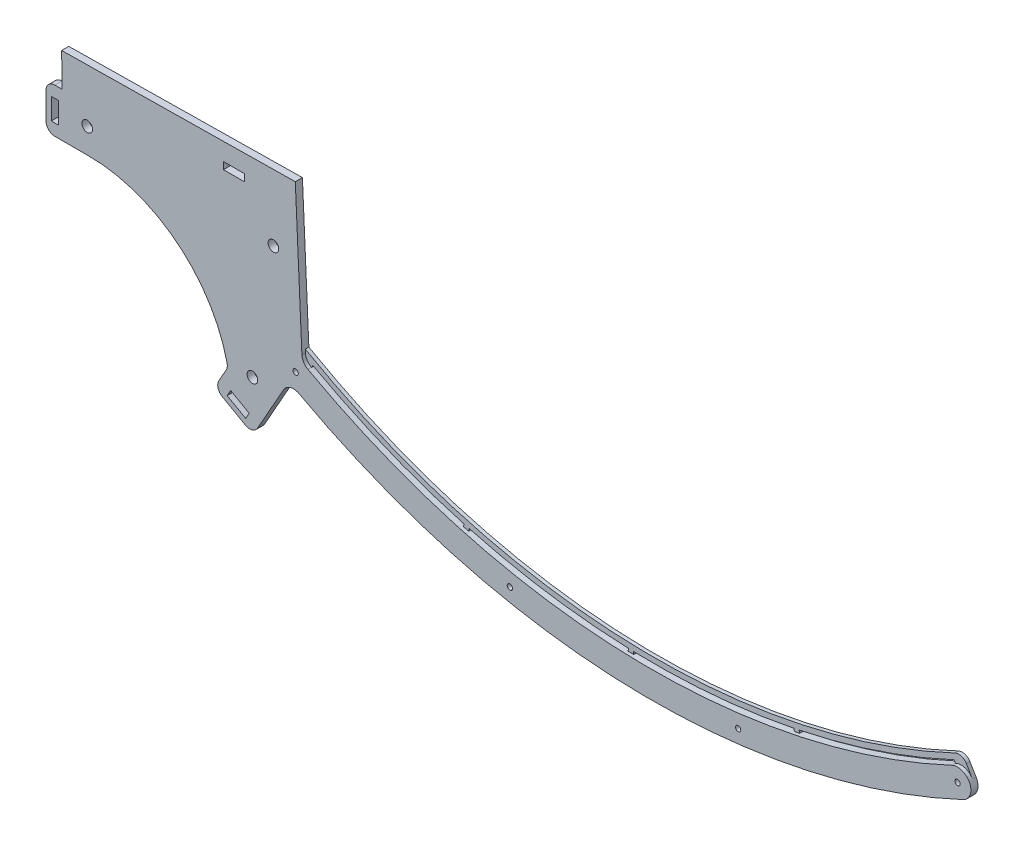
SolidWorks part; units mm, degrees
material "carbone"
ref_plane "Plan de face" through (0, 0, 0) normal (0, 0, 1) x (1, 0, 0)
ref_plane "Plan de dessus" through (0, 0, 0) normal (0, 1, 0) x (1, 0, 0)
ref_plane "Plan de droite" through (0, 0, 0) normal (1, 0, 0) x (0, 0, -1)
sketch "Esquisse1" plane through (0, 0, 0) normal (0, 0, 1) x (1, 0, 0)
  line L0 (-415, 0) -> (-385, 0) construction
  line L1 (-313.1067, -272.377) -> (70.5189, -272.377) construction
  line L2 (-313.1067, -272.377) -> (-15.9919, -246.3828) construction
  line L3 (-286.5711, -300.17) -> (75.0928, -268.5285) construction
  circle A0 centre (0, 0) radius 385 construction
  circle A1 centre (0, 0) radius 415 construction
  point P4 (-415, 0)
  point P5 (-192.2289, -367.7948)
  point P8 (-313.1067, -272.377)
  dimension "D1" = 830
  dimension "D2" = 30
  dimension "D3" = 430
  dimension "D4" = 154
  dimension "D5" = 5
  dimension "D6" = 30
sketch "Esquisse2" plane through (0, 0, 0) normal (0, 0, 1) x (1, 0, 0)
  line L0 (-317.1344, -294.0782) -> (-212.3002, -299.9748) construction
  line L1 (-203.4522, -361.7073) -> (0, 0) construction
  line L2 (-199.9716, -262.4789) -> (-196.0985, -348.6336)
  line L3 (-212.3002, -299.9748) -> (0, 0) construction
  line L4 (-313.1067, -272.377) -> (-15.9919, -246.3828) construction
  line L5 (-211.9204, -376.7625) -> (-203.4522, -361.7073)
  line L6 (180.3525, -357.0336) -> (187.1157, -370.4223)
  line L7 (-331.1331, -294.269) -> (-331.5419, -264.2717)
  line L8 (-331.5419, -264.2717) -> (-199.9716, -262.4789)
  line L9 (-317.1344, -294.0782) -> (0, 0) construction
  circle A0 centre (0, 0) radius 415 construction
  arc A1 (-203.4522, -361.7073) -> (187.1157, -370.4223) centre (0, 0) ccw
  arc A3 (-331.1331, -294.269) -> (-317.0174, -308.0777) centre (-317.1344, -294.0782) ccw
  arc A4 (-237.8584, -372.6061) -> (-211.9204, -376.7625) centre (-224.1226, -369.899) ccw
  circle A5 centre (-317.1344, -294.0782) radius 3
  circle A6 centre (-212.3002, -299.9748) radius 3
  circle A7 centre (-224.1226, -369.899) radius 3
  arc A8 (-317.0174, -308.0777) -> (-237.8584, -372.6061) centre (-316.3486, -388.0749) cw
  arc A9 (180.3525, -357.0336) -> (-196.0985, -348.6336) centre (0, 0) cw
  point P0 (-317.1344, -294.0782)
  point P1 (-224.1226, -369.899)
  point P2 (-212.3002, -299.9748)
  point P30 (-212.3002, -299.9748)
  dimension "D1" = 432.5
  dimension "D7" = 14
  dimension "D8" = 400
  dimension "D9" = 6
  dimension "D10" = 15
  dimension "D5" = 80
  dimension "D11" = 105
  dimension "D2" = 367.5
  dimension "D3" = 432.5
  dimension "D4" = 120
  dimension "D6" = 14
  dimension "D12" = 4
  dimension "D13" = 30
extrude "Boss.-Extru.1" add sketch "Esquisse2" along normal blind 4
sketch "Esquisse3" plane through (0, 0, 4) normal (0, 0, 1) x (1, 0, 0)
  line L0 (187.1157, -370.4223) -> (180.3525, -357.0336) construction
  line L1 (-199.9716, -262.4789) -> (-331.5419, -264.2717) construction
  line L2 (169.7604, -362.1897) -> (162.8772, -362.1897)
  line L3 (187.1157, -370.4223) -> (180.3525, -357.0336)
  line L4 (162.8772, -362.1897) -> (180.9651, -354.1521)
  line L5 (180.9651, -354.1521) -> (180.3525, -357.0336)
  line L6 (176.1264, -375.7718) -> (174.8535, -378.4751)
  line L7 (174.8535, -378.4751) -> (190.2868, -373.4747)
  line L8 (190.2868, -373.4747) -> (187.1157, -370.4223)
  line L9 (172.9434, -368.9808) -> (49.3529, -404.5004) construction
  line L10 (49.3529, -404.5004) -> (-79.1523, -399.7389) construction
  line L11 (-79.1523, -399.7389) -> (-199.7754, -355.1704) construction
  line L12 (-203.4522, -361.7073) -> (-196.0985, -348.6336) construction
  arc A0 (183.7341, -363.728) -> (-310.433, -263.9841) centre (0, 0) cw construction
  circle A1 centre (172.9434, -368.9808) radius 1.5
  arc A2 (169.7604, -362.1897) -> (176.1264, -375.7718) centre (172.9434, -368.9808) cw
  arc A3 (-196.0985, -348.6336) -> (180.3525, -357.0336) centre (0, 0) ccw construction
  arc A4 (-203.4522, -361.7073) -> (187.1157, -370.4223) centre (0, 0) ccw construction
  circle A5 centre (49.3529, -404.5004) radius 1.5
  circle A6 centre (-79.1523, -399.7389) radius 1.5
  circle A7 centre (-199.7754, -355.1704) radius 1.5
  dimension "D2" = 3
  dimension "D1" = 12
extrude "Enlèv. mat.-Extru.1" cut sketch "Esquisse3" against normal through all
fillet "Congé1" radius 6.5 2 edges at (-196.0985, -348.6336, 2) (-203.4522, -361.7073, 2)
sketch "Esquisse4" plane through (0, 0, 4) normal (0, 0, 1) x (1, 0, 0)
  line L0 (-211.9204, -376.7625) -> (-223.6864, -397.6805)
  line L1 (-211.9204, -376.7625) -> (-206.6143, -367.3289) construction
  line L2 (-223.6864, -397.6805) -> (-245.476, -385.4243)
  line L3 (-245.476, -385.4243) -> (-237.9656, -372.072)
  line L4 (-234.5812, -391.5524) -> (-232.1299, -387.1945) construction
  line L5 (-238.3399, -385.9962) -> (-227.8809, -391.8792)
  line L6 (-238.3399, -385.9962) -> (-236.3789, -382.5099)
  line L7 (-227.8809, -391.8792) -> (-225.9199, -388.3928)
  line L8 (-236.3789, -382.5099) -> (-225.9199, -388.3928)
  line L9 (-236.3789, -382.5099) -> (-227.8809, -391.8792) construction
  line L10 (-237.9656, -372.072) -> (-225.3743, -376.7625)
  line L11 (-225.3743, -376.7625) -> (-211.9204, -376.7625)
  line L12 (-316.3486, -308.0749) -> (-340.3486, -308.0749)
  line L13 (-340.3486, -308.0749) -> (-340.3486, -283.0749)
  line L14 (-340.3486, -283.0749) -> (-331.2857, -283.0749)
  line L15 (-331.5419, -264.2717) -> (-331.1331, -294.269) construction
  line L16 (-331.2857, -283.0749) -> (-316.3486, -308.0749)
  line L17 (-337.3486, -289.5749) -> (-337.3486, -301.5749)
  line L18 (-337.3486, -289.5749) -> (-333.3486, -289.5749)
  line L19 (-337.3486, -301.5749) -> (-333.3486, -301.5749)
  line L20 (-333.3486, -289.5749) -> (-333.3486, -301.5749)
  line L21 (-337.3486, -289.5749) -> (-333.3486, -301.5749) construction
  line L22 (-337.3486, -301.5749) -> (-333.3486, -289.5749) construction
  line L23 (-340.3486, -295.5749) -> (-335.3486, -295.5749) construction
  arc A0 (-237.8584, -372.6061) -> (-317.0174, -308.0777) centre (-316.3486, -388.0749) ccw construction
  point P12 (-232.1299, -387.1945)
  point P25 (-335.3486, -295.5749)
  dimension "D1" = 25
  dimension "D2" = 24
  dimension "D3" = 4
  dimension "D4" = 5
  dimension "D5" = 12
  dimension "D6" = 12
  dimension "D7" = 4
  dimension "D8" = 25
  dimension "D9" = 5
  dimension "D10" = 24
extrude "Boss.-Extru.2" add sketch "Esquisse4" against normal blind 4
fillet "Congé2" radius 5 5 edges at (-237.9656, -372.072, 2) (-245.476, -385.4243, 2) (-223.6864, -397.6805, 2) (-340.3486, -308.0749, 2) (-340.3486, -283.0749, 2)
sketch "Esquisse5" plane through (0, 0, 4) normal (0, 0, 1) x (1, 0, 0)
  line L0 (-196.2615, -345.0097) -> (-199.9716, -262.4789) construction
  line L1 (-240.45, -276.8679) -> (-228.45, -276.8679)
  line L2 (-240.45, -276.8679) -> (-240.45, -272.8679)
  line L3 (-240.45, -272.8679) -> (-228.45, -272.8679)
  line L4 (-228.45, -276.8679) -> (-228.45, -272.8679)
  line L5 (-240.45, -276.8679) -> (-228.45, -272.8679) construction
  line L6 (-240.45, -272.8679) -> (-228.45, -276.8679) construction
  line L7 (-199.9716, -262.4789) -> (-331.5419, -264.2717) construction
  point P0 (-234.45, -274.8679)
  dimension "D1" = 4
  dimension "D2" = 12
  dimension "D3" = 35
  dimension "D4" = 10
extrude "Enlèv. mat.-Extru.2" cut sketch "Esquisse5" against normal blind 4
sketch "Esquisse6" plane through (0, 0, 4) normal (0, 0, 1) x (1, 0, 0)
  line L0 (-196.2615, -345.0097) -> (-199.9716, -262.4789) construction
  line L1 (172.9434, -368.9808) -> (169.7604, -362.1897) construction
  line L2 (169.0038, -360.8878) -> (169.7604, -362.1897)
  line L3 (169.7604, -362.1897) -> (178.0421, -365.9221)
  line L4 (178.0421, -365.9221) -> (179.3749, -365.1225)
  line L5 (179.3749, -365.1225) -> (173.5385, -355.3936)
  line L6 (-196.3372, -343.3249) -> (-200.1827, -348.6234)
  line L7 (-194.0975, -353.3681) -> (-192.138, -349.1207)
  line L8 (-200.1827, -348.6234) -> (-194.0975, -353.3681)
  arc A0 (169.0038, -360.8878) -> (-192.138, -349.1207) centre (0, 0) cw
  arc A1 (-192.9027, -350.412) -> (169.7604, -362.1897) centre (0, 0) ccw construction
  arc A2 (176.1264, -375.7718) -> (169.7604, -362.1897) centre (172.9434, -368.9808) ccw construction
  arc A3 (-196.3372, -343.3249) -> (173.5385, -355.3936) centre (0, 0) ccw
  dimension "D1" = 1.5
  dimension "D2" = 3
extrude "Boss.-Extru.3" add sketch "Esquisse6" against normal up to surface (2 mm away) from offset 2 up to face at (-234.45, -274.8679, 0) offset against normal yes
fillet "Congé3" radius 5 1 edges at (173.5385, -355.3936, 1)
sketch "Esquisse8" plane through (0, 0, 0) normal (0, 0, -1) x (-1, 0, 0)
  line L0 (11.7062, -405.3338) -> (11.3806, -395.3391)
  line L1 (11.7062, -405.3338) -> (14.7046, -405.2361)
  line L2 (11.3806, -395.3391) -> (14.379, -395.2414)
  line L3 (14.7046, -405.2361) -> (14.379, -395.2414)
  line L4 (11.7062, -405.3338) -> (14.379, -395.2414) construction
  line L5 (11.3806, -395.3391) -> (14.7046, -405.2361) construction
  line L6 (-83.1017, -396.8962) -> (-81.0885, -387.101)
  line L7 (-83.1017, -396.8962) -> (-80.1631, -397.5002)
  line L8 (-81.0885, -387.101) -> (-78.15, -387.7049)
  line L9 (-80.1631, -397.5002) -> (-78.15, -387.7049)
  line L10 (-83.1017, -396.8962) -> (-78.15, -387.7049) construction
  line L11 (-81.0885, -387.101) -> (-80.1631, -397.5002) construction
  line L12 (105.8691, -391.4387) -> (103.2226, -381.7952)
  line L13 (105.8691, -391.4387) -> (108.7621, -390.6447)
  line L14 (103.2226, -381.7952) -> (106.1156, -381.0013)
  line L15 (108.7621, -390.6447) -> (106.1156, -381.0013)
  line L16 (105.8691, -391.4387) -> (106.1156, -381.0013) construction
  line L17 (103.2226, -381.7952) -> (108.7621, -390.6447) construction
  line L18 (13.2054, -405.2849) -> (12.8798, -395.2902) construction
  line L19 (-79.6192, -387.4029) -> (-81.6324, -397.1982) construction
  line L20 (104.6691, -381.3982) -> (107.3156, -391.0417) construction
  line L21 (-169.0038, -360.8878) -> (0, 0) construction
  line L22 (0, 0) -> (-79.6192, -387.4029) construction
  line L23 (12.8798, -395.2902) -> (0, 0) construction
  line L24 (0, 0) -> (104.6691, -381.3982) construction
  line L25 (192.138, -349.1207) -> (0, 0) construction
  line L26 (-91.1815, -194.7073) -> (-43.2823, -210.5983) construction
  line L27 (-43.2823, -210.5983) -> (7.0016, -214.886) construction
  line L28 (7.0016, -214.886) -> (56.8998, -207.3341) construction
  line L29 (56.8998, -207.3341) -> (103.6629, -188.3587) construction
  circle A0 centre (0, 0) radius 215 construction
  arc A3 (-169.4547, -357.3588) -> (196.3372, -343.3249) centre (0, 0) ccw construction
  point P0 (-80.6258, -392.3006)
  point P1 (13.0426, -400.2876)
  point P10 (105.9924, -386.22)
  point P31 (-91.1815, -194.7073)
  point P32 (-43.2823, -210.5983)
  point P33 (7.0016, -214.886)
  point P34 (56.8998, -207.3341)
  point P35 (103.6629, -188.3587)
  dimension "D3" = 430
  dimension "D1" = 3
  dimension "D2" = 10
extrude "Boss.-Extru.4" add sketch "Esquisse8" against normal up to surface (2 mm away) up to face at (-10.9827, -362.8718, 2)
